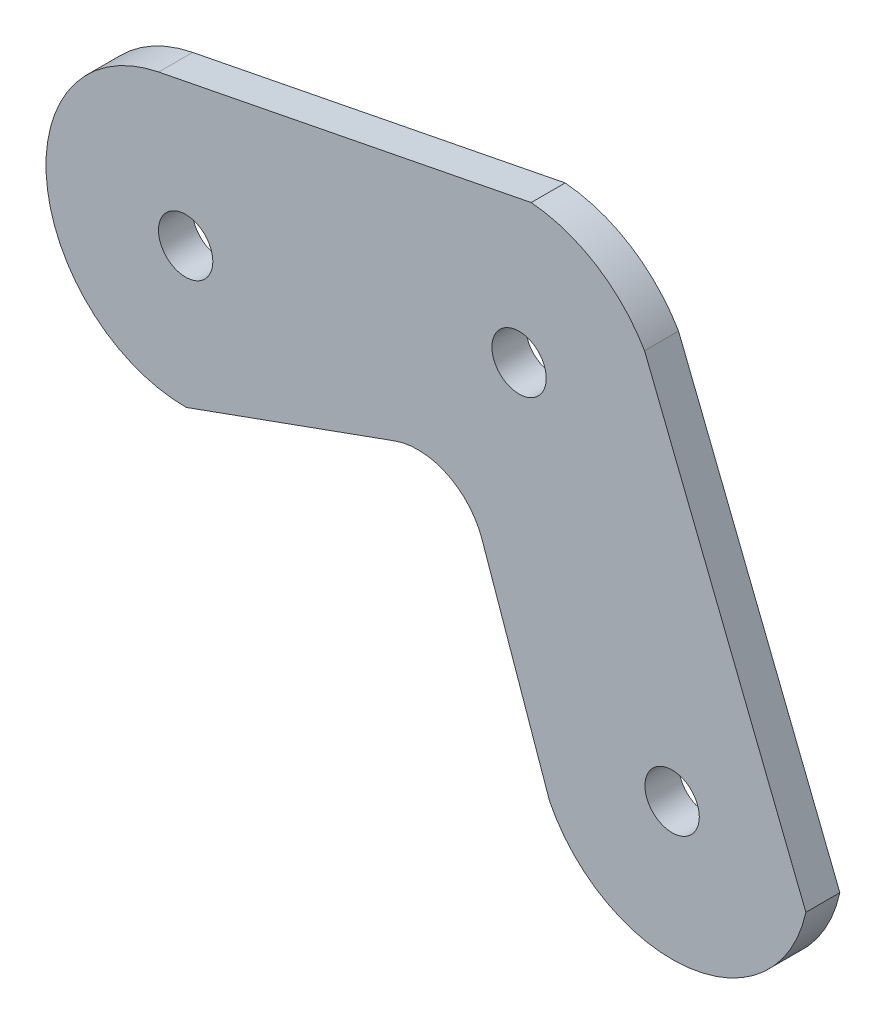
SolidWorks part; units mm, degrees
ref_plane "前视基准面" through (0, 0, 0) normal (0, 0, 1) x (1, 0, 0)
ref_plane "上视基准面" through (0, 0, 0) normal (0, 1, 0) x (1, 0, 0)
ref_plane "右视基准面" through (0, 0, 0) normal (1, 0, 0) x (0, 0, -1)
sketch "草图1" plane through (0, 0, 0) normal (0, 0, 1) x (1, 0, 0)
  line L0 (36.083, 65) -> (85.1444, 74.6422)
  line L1 (85.1444, 74.6422) -> (107.6628, 30)
  line L2 (107.6628, 30) -> (36.083, 65)
  line L3 (0, 0) -> (0, 252.2874)
  line L4 (0, 0) -> (398.1835, 0)
  line L5 (0, 0) -> (50, 0)
  line L6 (50, 0) -> (50, -60.1662)
  line L7 (32.1201, 85.1637) -> (86.9275, 95.9352)
  line L8 (103.6094, 85.3947) -> (127.3443, 25.7012)
  line L9 (36.1784, 44.4508) -> (66.8528, 55.5221)
  line L10 (79.6864, 49.4192) -> (89.6144, 21.0504)
  circle A0 centre (107.6628, 30) radius 4
  circle A1 centre (85.1444, 74.6422) radius 4
  circle A2 centre (36.083, 65) radius 4
  arc A3 (32.1201, 85.1637) -> (36.1784, 44.4508) centre (36.083, 65) ccw
  arc A4 (103.6094, 85.3947) -> (86.9275, 95.9352) centre (85.1444, 74.6422) ccw
  arc A5 (89.6144, 21.0504) -> (127.3443, 25.7012) centre (107.6628, 30) ccw
  arc A6 (66.8528, 55.5221) -> (79.6864, 49.4192) centre (70.2477, 46.116) cw
  point P2 (0, 0)
  dimension "D2" = 50
  dimension "D7" = 10
  dimension "D1" = 30
  dimension "D3" = 50
  dimension "D4" = 50
  dimension "D5" = 65
  dimension "D6" = 65
extrude "凸台-拉伸1" add sketch "草图1" along normal blind 5 contours L10 A5 L8 A4 L7 A3 L9 L2 A2 L0 A1 L1 A0 | L9 A6 L10 L2 A0 L1 A1 L0 A2
